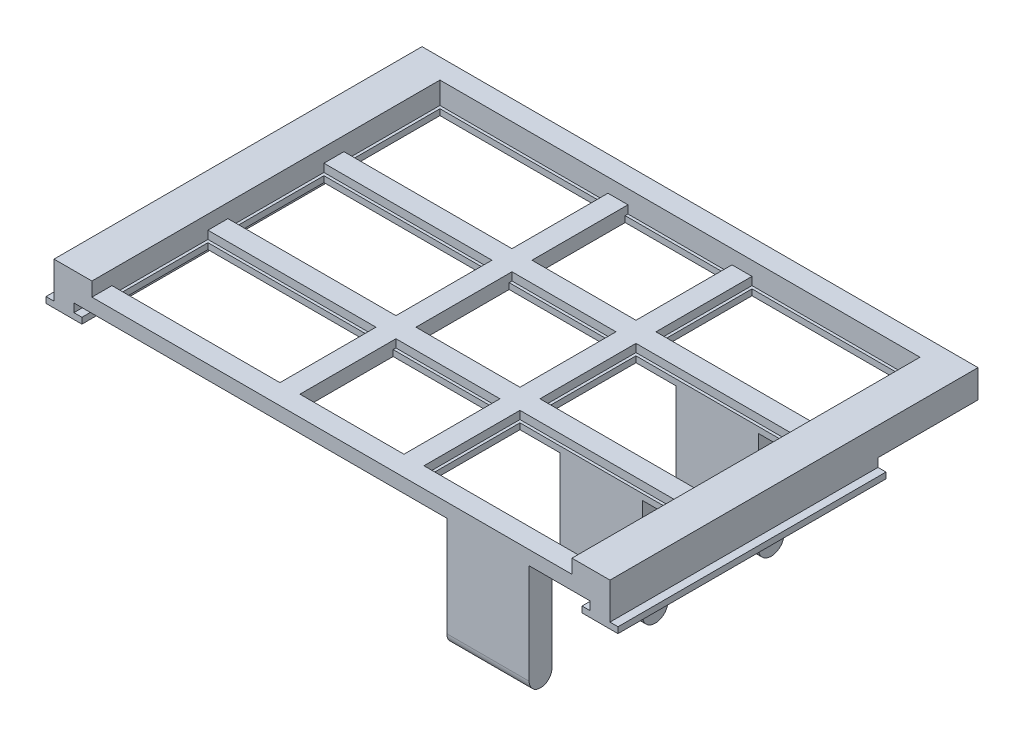
SolidWorks part; units mm, degrees
ref_plane "Front Plane" through (0, 0, 0) normal (0, 0, 1) x (1, 0, 0)
ref_plane "Top Plane" through (0, 0, 0) normal (0, 1, 0) x (1, 0, 0)
ref_plane "Right Plane" through (0, 0, 0) normal (1, 0, 0) x (0, 0, -1)
sketch "Sketch1" plane through (0, 0, 0) normal (0, 1, 0) x (1, 0, 0)
  line L0 (36.2173, -16.1456) -> (36.2173, 113.8544)
  line L1 (50.2173, -6.1456) -> (50.2173, 103.8544)
  line L2 (170.2173, -6.1456) -> (170.2173, 103.8544)
  line L3 (184.2173, -16.1456) -> (184.2173, 113.8544)
  line L4 (36.2173, 113.8544) -> (184.2173, 113.8544)
  line L5 (184.2173, -16.1456) -> (36.2173, -16.1456)
  line L10 (50.2173, 103.8544) -> (170.2173, 103.8544)
  line L12 (170.2173, -6.1456) -> (50.2173, -6.1456)
  line L14 (46.2173, 103.8544) -> (174.2173, 103.8544) construction
  line L15 (174.2173, -6.1456) -> (46.2173, -6.1456) construction
  line L16 (50.2173, -16.1456) -> (50.2173, 113.8544) construction
  line L17 (170.2173, -16.1456) -> (170.2173, 113.8544) construction
  line L18 (46.2173, -6.1456) -> (46.2173, 103.8544) construction
  line L19 (174.2173, -6.1456) -> (174.2173, 103.8544) construction
  line L20 (50.2173, 79.8544) -> (170.2173, 79.8544)
  line L24 (74.2173, 17.8544) -> (74.2173, 79.8544) construction
  line L25 (146.2173, 17.8544) -> (146.2173, 79.8544) construction
  line L26 (146.2173, 17.8544) -> (74.2173, 17.8544) construction
  line L27 (74.2173, 79.8544) -> (146.2173, 79.8544) construction
  line L28 (50.2173, 74.8544) -> (170.2173, 74.8544)
  line L29 (50.2173, 50.8544) -> (170.2173, 50.8544)
  line L30 (50.2173, 45.8544) -> (170.2173, 45.8544)
  line L31 (50.2173, 21.8544) -> (170.2173, 21.8544)
  line L32 (50.2173, 16.8544) -> (170.2173, 16.8544)
  dimension "D1" = 14
  dimension "D2" = 134
  dimension "D3" = 24
  dimension "D4" = 10
  dimension "D5" = 5
  dimension "D6" = 29
  dimension "D7" = 29
extrude "Boss-Extrude2" add sketch "Sketch1" along normal blind 10 contours L5 L3 L4 L0 L2 L12 L1 L10
sketch "Sketch2" plane through (0, 0, 0) normal (0, -1, 0) x (1, 0, 0)
  line L0 (50.2173, -103.8544) -> (170.2173, -103.8544)
  line L1 (50.2173, -103.8544) -> (170.2173, -103.8544) construction
  line L2 (50.2173, 6.1456) -> (170.2173, 6.1456)
  line L3 (170.2173, 6.1456) -> (170.2173, -103.8544) construction
  line L4 (170.2173, 6.1456) -> (50.2173, 6.1456) construction
  line L5 (50.2173, -103.8544) -> (50.2173, 6.1456)
  line L6 (50.2173, 6.1456) -> (50.2173, -103.8544) construction
  line L7 (170.2173, -103.8544) -> (170.2173, 6.1456)
  line L8 (74.2173, -79.8544) -> (146.2173, -79.8544) construction
  line L9 (50.2173, -79.8544) -> (170.2173, -79.8544)
  line L10 (50.2173, -74.8544) -> (170.2173, -74.8544)
  line L11 (74.2173, -79.8544) -> (74.2173, 6.1456) construction
  line L12 (146.2173, -79.8544) -> (146.2173, 6.1456) construction
  line L13 (50.2173, -50.8544) -> (170.2173, -50.8544)
  line L14 (50.2173, -45.8544) -> (170.2173, -45.8544)
  line L15 (50.2173, -21.8544) -> (170.2173, -21.8544)
  line L16 (50.2173, -16.8544) -> (170.2173, -16.8544)
  line L17 (50.9173, -103.1544) -> (169.5173, -103.1544)
  line L18 (169.5173, -103.1544) -> (169.5173, -80.5544)
  line L19 (50.9173, 5.4456) -> (169.5173, 5.4456)
  line L20 (50.9173, -103.1544) -> (50.9173, -80.5544)
  line L21 (50.9173, -74.1544) -> (169.5173, -74.1544)
  line L22 (50.9173, -45.1544) -> (169.5173, -45.1544)
  line L23 (50.9173, -16.1544) -> (169.5173, -16.1544)
  line L24 (50.9173, -80.5544) -> (169.5173, -80.5544)
  line L25 (50.9173, -51.5544) -> (169.5173, -51.5544)
  line L26 (50.9173, -22.5544) -> (169.5173, -22.5544)
  line L27 (50.9173, -74.1544) -> (50.9173, -51.5544)
  line L28 (50.9173, -103.1544) -> (50.9173, 5.4456) construction
  line L29 (50.2173, -74.1544) -> (170.2173, -74.1544) construction
  line L30 (50.2173, -80.5544) -> (170.2173, -80.5544) construction
  line L31 (169.5173, -74.1544) -> (169.5173, -51.5544)
  line L32 (169.5173, -103.1544) -> (169.5173, 5.4456) construction
  line L33 (50.2173, -51.5544) -> (170.2173, -51.5544) construction
  line L34 (169.5173, -45.1544) -> (169.5173, -22.5544)
  line L35 (50.2173, -45.1544) -> (170.2173, -45.1544) construction
  line L36 (50.9173, -45.1544) -> (50.9173, -22.5544)
  line L37 (50.2173, -22.5544) -> (170.2173, -22.5544) construction
  line L38 (169.5173, -16.1544) -> (169.5173, 5.4456)
  line L39 (50.2173, -16.1544) -> (170.2173, -16.1544) construction
  line L40 (50.9173, -16.1544) -> (50.9173, 5.4456)
  line M22 (170.2173, 6.1456) -> (170.2173, -103.8544)
  line M23 (170.2173, -103.8544) -> (50.2173, -103.8544)
  line M24 (50.2173, -103.8544) -> (50.2173, 6.1456)
  line M25 (50.2173, 6.1456) -> (170.2173, 6.1456)
  dimension "D1" = 24
  dimension "D2" = 5
  dimension "D3" = 29
  dimension "D4" = 29
  dimension "D5" = 0.7
  dimension "D6" = 0.7
extrude "Boss-Extrude3" add sketch "Sketch2" against normal blind 1.5 contours L9 L7 L20 L24 L18 L17 M24 M23 | L13 L10 L7 L31 L21 L27 L25 M24 | L15 L14 L7 L22 L36 L26 L34 M24 | L16 L23 L40 L19 L38 M24 M22 M25 | L16 L5 L15 L7 | L14 L5 L13 L7 | L10 L5 L9 L7
sketch "Sketch3" plane through (0, 1.5, 0) normal (0, 1, 0) x (1, 0, 0)
  line L0 (50.2173, 74.8544) -> (170.2173, 74.8544)
  line L3 (50.2173, 79.8544) -> (170.2173, 79.8544)
  line L4 (50.2173, 79.8544) -> (50.2173, 74.8544)
  line L5 (170.2173, 79.8544) -> (170.2173, 74.8544)
  line L6 (50.2173, 45.8544) -> (50.2173, 50.8544)
  line L9 (170.2173, 45.8544) -> (50.2173, 45.8544)
  line L10 (50.2173, 103.8544) -> (50.2173, -6.1456) construction
  line L11 (170.2173, 45.8544) -> (170.2173, 50.8544)
  line L12 (170.2173, -6.1456) -> (170.2173, 103.8544) construction
  line L13 (170.2173, 50.8544) -> (50.2173, 50.8544)
  line L14 (50.2173, 16.8544) -> (50.2173, 21.8544)
  line L16 (170.2173, 16.8544) -> (50.2173, 16.8544)
  line L17 (170.2173, 16.8544) -> (170.2173, 21.8544)
  line L18 (170.2173, -6.1456) -> (170.2173, 103.8544) construction
  line L19 (170.2173, 21.8544) -> (50.2173, 21.8544)
  dimension "D1" = 5
extrude "Boss-Extrude4" add sketch "Sketch3" along normal blind 2 contours L19 L14 L16 L17 | L13 L6 L9 L11 | L5 L0 L4 L3
sketch "Sketch4" plane through (0, 0, 0) normal (0, -1, 0) x (-1, 0, 0)
  line L0 (-50.2173, 103.8544) -> (-50.2173, -6.1456)
  line L1 (-170.2173, -6.1456) -> (-50.2173, -6.1456) construction
  line L2 (-50.2173, -6.1456) -> (-50.2173, 103.8544) construction
  line L3 (-92.2173, 103.8544) -> (-92.2173, -6.1456)
  line L4 (-87.2173, 103.8544) -> (-87.2173, -6.1456)
  line L5 (-87.2173, 103.8544) -> (-92.2173, 103.8544)
  line L6 (-92.2173, -6.1456) -> (-87.2173, -6.1456)
  line L7 (-170.2173, -6.1456) -> (-170.2173, 103.8544)
  line L8 (-128.2173, -6.1456) -> (-128.2173, 103.8544)
  line L9 (-123.2173, -6.1456) -> (-123.2173, 103.8544)
  line L10 (-123.2173, 103.8544) -> (-128.2173, 103.8544)
  line L11 (-128.2173, -6.1456) -> (-123.2173, -6.1456)
  dimension "D1" = 42
  dimension "D2" = 5
  dimension "D3" = 42
  dimension "D4" = 5
extrude "Boss-Extrude5" add sketch "Sketch4" against normal blind 3.5 contours L4 L6 L3 L5 | L9 L10 L8 L11
sketch "Sketch5" plane through (0, 0, 0) normal (0, -1, 0) x (-1, 0, 0)
  line L1 (-92.2173, 80.5544) -> (-92.2173, 103.1544)
  line L2 (-92.2173, 103.1544) -> (-87.2173, 103.1544)
  line L14 (-87.2173, 16.1544) -> (-92.2173, 16.1544)
  line L15 (-92.2173, 16.8544) -> (-92.2173, -6.1456) construction
  line L16 (-92.2173, 16.1544) -> (-92.2173, -5.4456)
  line L17 (-92.2173, -5.4456) -> (-87.2173, -5.4456)
  line L18 (-87.2173, 16.8544) -> (-87.2173, -6.1456) construction
  line L19 (-87.2173, -5.4456) -> (-87.2173, 16.1544)
  line L21 (-87.2173, 22.5544) -> (-92.2173, 22.5544)
  line L22 (-92.2173, 22.5544) -> (-92.2173, 45.1544)
  line L23 (-92.2173, 45.1544) -> (-87.2173, 45.1544)
  line L24 (-87.2173, 103.1544) -> (-87.2173, 80.5544)
  line L25 (-87.2173, 22.5544) -> (-87.2173, 45.1544)
  line L26 (-87.2173, 51.5544) -> (-92.2173, 51.5544)
  line L27 (-92.2173, 51.5544) -> (-92.2173, 74.1544)
  line L28 (-92.2173, 74.1544) -> (-87.2173, 74.1544)
  line L29 (-87.2173, 74.1544) -> (-87.2173, 51.5544)
  line L30 (-87.2173, 80.5544) -> (-92.2173, 80.5544)
extrude "Cut-Extrude1" cut sketch "Sketch5" against normal blind 10
sketch "Sketch6" plane through (0, 1.5, 0) normal (0, 1, 0) x (1, 0, 0)
  line L0 (87.2173, 103.8544) -> (92.2173, 103.8544)
  line L1 (92.2173, 103.8544) -> (92.2173, 103.1544)
  line L2 (92.2173, 103.8544) -> (92.2173, 103.1544) construction
  line L3 (92.2173, 103.1544) -> (87.2173, 103.1544) construction
  line L4 (92.2173, 103.1544) -> (87.2173, 103.1544)
  line L5 (87.2173, 103.1544) -> (87.2173, 103.8544)
  line L6 (92.2173, 80.5544) -> (87.2173, 80.5544)
  line L7 (87.2173, 80.5544) -> (87.2173, 79.8544)
  line L8 (87.2173, 79.8544) -> (92.2173, 79.8544)
  line L9 (92.2173, 79.8544) -> (92.2173, 80.5544)
  line L10 (87.2173, 74.8544) -> (92.2173, 74.8544)
  line L11 (92.2173, 74.8544) -> (92.2173, 74.1544)
  line L12 (92.2173, 74.1544) -> (87.2173, 74.1544) construction
  line L13 (92.2173, 74.1544) -> (123.2173, 74.1544) construction
  line L14 (92.2173, 74.1544) -> (87.2173, 74.1544)
  line L15 (87.2173, 74.8544) -> (87.2173, 74.1544) construction
  line L16 (87.2173, 74.1544) -> (87.2173, 74.8544)
  line L17 (87.2173, 51.5544) -> (92.2173, 51.5544)
  line L18 (92.2173, 51.5544) -> (92.2173, 50.8544)
  line L19 (92.2173, 50.8544) -> (87.2173, 50.8544)
  line L20 (87.2173, 50.8544) -> (87.2173, 51.5544)
  line L21 (92.2173, 45.8544) -> (87.2173, 45.8544)
  line L22 (87.2173, 45.8544) -> (87.2173, 45.1544)
  line L23 (92.2173, 45.1544) -> (87.2173, 45.1544) construction
  line L24 (87.2173, 45.1544) -> (92.2173, 45.1544)
  line L25 (92.2173, 45.1544) -> (92.2173, 45.8544)
  line L26 (87.2173, 22.5544) -> (92.2173, 22.5544)
  line L27 (92.2173, 22.5544) -> (92.2173, 21.8544)
  line L28 (92.2173, 21.8544) -> (87.2173, 21.8544)
  line L29 (87.2173, 21.8544) -> (87.2173, 22.5544)
  line L30 (87.2173, 16.8544) -> (92.2173, 16.8544)
  line L31 (92.2173, 16.8544) -> (92.2173, 16.1544)
  line L32 (92.2173, 16.1544) -> (87.2173, 16.1544) construction
  line L33 (92.2173, 16.1544) -> (87.2173, 16.1544)
  line L34 (87.2173, 16.8544) -> (87.2173, 16.1544) construction
  line L35 (87.2173, 16.1544) -> (87.2173, 16.8544)
  line L36 (87.2173, -5.4456) -> (92.2173, -5.4456)
  line L37 (92.2173, -5.4456) -> (92.2173, -6.1456)
  line L38 (92.2173, -6.1456) -> (87.2173, -6.1456)
  line L39 (87.2173, -6.1456) -> (87.2173, -5.4456)
extrude "Cut-Extrude2" cut sketch "Sketch6" along normal blind 2
sketch "Sketch7" plane through (0, 0, 0) normal (0, -1, 0) x (-1, 0, 0)
  line L0 (-92.2173, 79.8544) -> (-97.2173, 79.8544)
  line L3 (-92.2173, 103.8544) -> (-92.2173, 79.8544)
  line L4 (-97.2173, 103.8544) -> (-97.2173, 79.8544)
  line L5 (-97.2173, 103.8544) -> (-92.2173, 103.8544)
  line L6 (-92.2173, 74.8544) -> (-92.2173, 50.8544)
  line L7 (-97.2173, 74.8544) -> (-97.2173, 50.8544)
  line L8 (-92.2173, 50.8544) -> (-97.2173, 50.8544)
  line L9 (-97.2173, 74.8544) -> (-92.2173, 74.8544)
  line L10 (-97.2173, 16.8544) -> (-97.2173, -6.1456)
  line L11 (-97.2173, 16.8544) -> (-92.2173, 16.8544)
  line L12 (-92.2173, 21.8544) -> (-97.2173, 21.8544)
  line L13 (-97.2173, 45.8544) -> (-92.2173, 45.8544)
  line L15 (-97.2173, 45.8544) -> (-97.2173, 21.8544)
  line L16 (-92.2173, 16.8544) -> (-92.2173, -6.1706)
  line L17 (-92.2173, 45.8544) -> (-92.2173, 21.8544)
  line L18 (-92.2173, -6.1706) -> (-97.2173, -6.1456)
  line L19 (-50.2173, -6.1456) -> (-123.2173, -6.1456) construction
  dimension "D2" = 5
extrude "Boss-Extrude7" add sketch "Sketch7" against normal blind 3.5
sketch "Sketch8" plane through (0, 0, 0) normal (0, -1, 0) x (-1, 0, 0)
  line L0 (-92.2173, 103.1544) -> (-92.2173, 80.5544)
  line L1 (-92.2173, 103.1544) -> (-91.5173, 103.1544)
  line L2 (-50.9173, 103.1544) -> (-92.2173, 103.1544) construction
  line L3 (-91.5173, 103.1544) -> (-91.5173, 80.5544)
  line L4 (-50.9173, 80.5544) -> (-92.2173, 80.5544) construction
  line L5 (-91.5173, 80.5544) -> (-92.2173, 80.5544)
  line L6 (-91.5173, 74.1544) -> (-91.5173, 51.5544)
  line L7 (-92.2173, 74.1544) -> (-91.5173, 74.1544)
  line L8 (-91.5173, 51.5544) -> (-92.2173, 51.5544)
  line L9 (-92.2173, 74.1544) -> (-92.2173, 51.5544)
  line L10 (-91.5173, 22.5544) -> (-92.2173, 22.5544)
  line L11 (-92.2173, 45.1544) -> (-92.2173, 22.5544)
  line L12 (-92.2173, 45.1544) -> (-91.5173, 45.1544)
  line L13 (-91.5173, 45.1544) -> (-91.5173, 22.5544)
extrude "Boss-Extrude8" add sketch "Sketch8" against normal blind 1.5
sketch "Sketch9" plane through (0, 0, 0) normal (0, -1, 0) x (-1, 0, 0)
  line L14 (-50.2173, 16.8544) -> (-92.2173, 16.8544)
  line L15 (-170.2173, -6.1456) -> (-170.2173, 103.8544) construction
  line L16 (-170.2173, 16.8544) -> (-128.2173, 16.8544) construction
  line L36 (-170.2173, -6.1456) -> (-128.2173, -6.1456)
  line L37 (-50.2173, -6.1456) -> (-92.2173, -6.1456) construction
  line L40 (-170.2173, -6.1456) -> (-50.2173, -6.1456) construction
  line L41 (-170.2173, -6.1456) -> (-170.2173, 16.8544)
  line L42 (-50.2173, 16.8544) -> (-50.2173, -6.1456)
  line L43 (-50.9173, 16.1544) -> (-92.2173, 16.1544)
  line L44 (-92.2173, 16.1544) -> (-92.2173, 16.8544)
  line L45 (-92.2173, -6.1456) -> (-92.2173, -5.4456)
  line L46 (-92.2173, -5.4456) -> (-50.9173, -5.4456)
  line L47 (-50.9173, -5.4456) -> (-50.9173, 16.1544)
  line L48 (-97.2173, 16.8544) -> (-97.2173, 16.1544)
  line L49 (-97.2173, 16.1544) -> (-123.2173, 16.1544)
  line L50 (-123.2173, 16.1544) -> (-123.2173, 16.8544)
  line L51 (-123.2173, -5.4456) -> (-97.2173, -5.4456)
  line L52 (-97.2173, -5.4456) -> (-97.2173, -6.1456)
  line L53 (-97.2173, 16.8544) -> (-97.2173, -6.1456) construction
  line L54 (-97.2173, -6.1456) -> (-123.2173, -6.1456)
  line L55 (-123.2173, -6.1456) -> (-123.2173, 16.8544) construction
  line L56 (-123.2173, -6.1456) -> (-123.2173, -5.4456)
  line L57 (-128.2173, 16.8544) -> (-128.2173, 16.1544)
  line L58 (-128.2173, 16.1544) -> (-169.5173, 16.1544)
  line L59 (-169.5173, 16.1544) -> (-169.5173, -5.4456)
  line L60 (-169.5173, -5.4456) -> (-128.2173, -5.4456)
  line L61 (-128.2173, -5.4456) -> (-128.2173, -6.1456)
  line L62 (-97.2173, 16.8544) -> (-123.2173, 16.8544)
  line L63 (-92.2173, -6.1456) -> (-50.2173, -6.1456)
  line L65 (-128.2173, 16.8544) -> (-170.2173, 16.8544)
extrude "Cut-Extrude3" cut sketch "Sketch9" against normal blind 1.5
sketch "Sketch10" plane through (0, 0, 0) normal (0, -1, 0) x (-1, 0, 0)
  line L0 (-128.2173, 103.1544) -> (-128.2173, 80.5544)
  line L1 (-128.2173, 103.1544) -> (-128.9173, 103.1544)
  line L2 (-128.2173, 103.1544) -> (-169.5173, 103.1544) construction
  line L3 (-128.2173, 80.5544) -> (-128.9173, 80.5544)
  line L4 (-128.2173, 80.5544) -> (-169.5173, 80.5544) construction
  line L5 (-128.9173, 80.5544) -> (-128.9173, 103.1544)
  line L6 (-128.9173, 51.5544) -> (-128.9173, 74.1544)
  line L7 (-128.2173, 74.1544) -> (-128.2173, 51.5544)
  line L8 (-128.2173, 51.5544) -> (-128.9173, 51.5544)
  line L9 (-128.2173, 74.1544) -> (-128.9173, 74.1544)
  line L10 (-128.2173, 22.5544) -> (-128.9173, 22.5544)
  line L11 (-128.9173, 22.5544) -> (-128.9173, 45.1544)
  line L12 (-128.2173, 45.1544) -> (-128.2173, 22.5544)
  line L13 (-128.2173, 45.1544) -> (-128.9173, 45.1544)
extrude "Boss-Extrude9" add sketch "Sketch10" against normal blind 1.5
sketch "Sketch11" plane through (0, 0, 0) normal (0, -1, 0) x (-1, 0, 0)
  line L0 (-45.7173, 13.8544) -> (-45.7173, 83.8544)
  line L1 (-40.7173, 13.8544) -> (-40.7173, 83.8544)
  line L2 (-179.7173, 13.8544) -> (-179.7173, 83.8544)
  line L8 (-40.7173, 13.8544) -> (-45.7173, 13.8544)
  line L9 (-40.7173, 83.8544) -> (-45.7173, 83.8544)
  line L10 (-40.7173, -16.1456) -> (-40.7173, 113.8544) construction
  line L11 (-45.7173, -16.1456) -> (-45.7173, 113.8544) construction
  line L12 (-174.7173, 13.8544) -> (-174.7173, 83.8544)
  line L13 (-174.7173, 13.8544) -> (-179.7173, 13.8544)
  line L14 (-174.7173, 83.8544) -> (-179.7173, 83.8544)
extrude "Boss-Extrude10" add sketch "Sketch11" along normal blind 3
sketch "Sketch12" plane through (0, 10, 0) normal (0, 1, 0) x (1, 0, 0)
  line L4 (36.2173, -16.1456) -> (40.7367, -16.1456)
  line L12 (184.2173, -16.1456) -> (36.2173, -16.1456) construction
  line L13 (40.7367, -16.1456) -> (40.7367, 113.8544)
  line L14 (36.2173, 113.8544) -> (184.2173, 113.8544) construction
  line L15 (40.7367, 113.8544) -> (36.2173, 113.8544)
  line L16 (36.2173, 113.8544) -> (36.2173, -16.1456)
  line L17 (184.2173, -16.1456) -> (179.7173, -16.1456)
  line L18 (179.7173, -16.1456) -> (179.7173, 113.8544)
  line L19 (179.7173, 113.8544) -> (184.2173, 113.8544)
  line L20 (184.2173, 113.8544) -> (184.2173, -16.1456)
extrude "Cut-Extrude4" cut sketch "Sketch12" against normal blind 20
sketch "Sketch13" plane through (0, 0, 0) normal (0, -1, 0) x (-1, 0, 0)
  line L0 (-40.7367, 13.8544) -> (-179.7173, 13.8544)
  line L1 (-179.7173, 13.8544) -> (-179.7173, -16.1456)
  line L2 (-179.7173, -16.1456) -> (-40.7367, -16.1456)
  line L3 (-40.7367, -16.1456) -> (-40.7367, 13.8544)
  line L4 (-40.7367, 113.8544) -> (-40.7367, 108.8544)
  line L5 (-40.7367, 83.8544) -> (-40.7367, 113.8544) construction
  line L6 (-40.7367, 108.8544) -> (-179.7173, 108.8544)
  line L7 (-179.7173, 113.8544) -> (-179.7173, 83.8544) construction
  line L8 (-179.7173, 108.8544) -> (-179.7173, 113.8544)
  line L9 (-179.7173, 113.8544) -> (-40.7367, 113.8544)
extrude "Cut-Extrude5" cut sketch "Sketch13" against normal blind 20
sketch "Sketch14" plane through (0, 0, 0) normal (0, -1, 0) x (-1, 0, 0)
  line L0 (-179.7173, 16.8544) -> (-40.7367, 16.8544)
  line L1 (-179.7173, 83.8544) -> (-179.7173, 13.8544) construction
  line L2 (-40.7367, 13.8544) -> (-40.7367, 83.8544) construction
  line L3 (-40.7367, 16.8544) -> (-40.7367, 13.8544)
  line L4 (-40.7367, 13.8544) -> (-179.7173, 13.8544)
  line L5 (-179.7173, 13.8544) -> (-179.7173, 16.8544)
extrude "Cut-Extrude6" cut sketch "Sketch14" against normal blind 20
sketch "Sketch15" plane through (0, -3, 0) normal (0, -1, 0) x (-1, 0, 0)
  line L0 (-45.7173, 16.8544) -> (-40.7367, 16.8544)
  line L1 (-40.7367, 16.8544) -> (-40.7367, 13.8544)
  line L2 (-40.7367, 13.8544) -> (-45.7173, 13.8544)
  line L3 (-45.7173, 13.8544) -> (-40.7367, 13.8544) construction
  line L4 (-45.7173, 83.8544) -> (-45.7173, 13.8544) construction
  line L5 (-45.7173, 13.8544) -> (-45.7173, 16.8544)
  line L6 (-174.7173, 16.8544) -> (-179.7173, 16.8544)
  line L7 (-179.7173, 83.8544) -> (-179.7173, 13.8544) construction
  line L8 (-179.7173, 16.8544) -> (-179.7173, 13.8544)
  line L9 (-179.7173, 13.8544) -> (-174.7173, 13.8544)
  line L10 (-179.7173, 13.8544) -> (-174.7173, 13.8544) construction
  line L11 (-174.7173, 13.8544) -> (-174.7173, 83.8544) construction
  line L12 (-174.7173, 13.8544) -> (-174.7173, 16.8544)
extrude "Cut-Extrude7" cut sketch "Sketch15" against normal blind 20
sketch "Sketch16" plane through (0, 0, -16.8544) normal (0, 0, 1) x (1, 0, 0)
  line L0 (40.7367, 10) -> (40.7367, 7)
  line L2 (40.7367, -3) -> (40.7367, 10) construction
  line L3 (40.7367, 7) -> (179.7173, 7)
  line L4 (179.7173, 10) -> (179.7173, -3) construction
  line L5 (179.7173, 7) -> (179.7173, 10)
  line L6 (179.7173, 10) -> (40.7367, 10)
extrude "Cut-Extrude8" cut sketch "Sketch16" against normal blind 200
sketch "Sketch17" plane through (0, 0, 0) normal (0, -1, 0) x (-1, 0, 0)
  line L0 (-138.9173, 74.1544) -> (-159.5173, 74.1544)
  line L1 (-138.9173, 74.1544) -> (-138.9173, 80.5544)
  line L2 (-159.5173, 80.5544) -> (-138.9173, 80.5544)
  line L4 (-159.5173, 74.1544) -> (-159.5173, 80.5544)
  line L5 (-159.5173, 45.1544) -> (-159.5173, 51.5544)
  line L6 (-138.9173, 45.1544) -> (-138.9173, 51.5544)
  line L7 (-159.5173, 51.5544) -> (-138.9173, 51.5544)
  line L8 (-138.9173, 45.1544) -> (-159.5173, 45.1544)
  line L9 (-159.5173, 16.8544) -> (-159.5173, 22.5544)
  line L11 (-138.9173, 16.8544) -> (-138.9173, 22.5544)
  line L12 (-138.9173, 16.8544) -> (-159.5173, 16.8544)
  line L13 (-138.9173, 22.5544) -> (-159.5173, 22.5544)
  line L14 (-128.9173, 22.5544) -> (-169.5173, 22.5544) construction
extrude "Boss-Extrude11" add sketch "Sketch17" along normal blind 10
sketch "Sketch18" plane through (138.9173, 0, 0) normal (-1, 0, 0) x (0, 0, 1)
  line L0 (-16.8544, -10) -> (-22.5544, -10) construction
  line L1 (-45.1544, -10) -> (-51.5544, -10) construction
  line L2 (-74.1544, -10) -> (-80.5544, -10) construction
  line L3 (-22.5544, -10) -> (-16.8544, -10)
  line L4 (-45.1544, -10) -> (-51.5544, -10)
  line L5 (-74.1544, -10) -> (-80.5544, -10)
  arc A0 (-22.5544, -10) -> (-16.8544, -10) centre (-19.7044, -10) ccw
  arc A1 (-51.5544, -10) -> (-45.1544, -10) centre (-48.3544, -10) ccw
  arc A2 (-80.5544, -10) -> (-74.1544, -10) centre (-77.3544, -10) ccw
extrude "Boss-Extrude12" add sketch "Sketch18" against normal blind 20.6
sketch "Sketch19" plane through (138.9173, 0, 0) normal (-1, 0, 0) x (0, 0, 1)
  line L0 (-16.8544, -10) -> (-16.8544, -25)
  line L1 (-22.5544, -10) -> (-22.5544, -25)
  line L2 (-45.1544, -10) -> (-45.1544, -25)
  line L3 (-51.5544, -10) -> (-51.5544, -25)
  line L4 (-74.1544, -10) -> (-74.1544, -25)
  line L5 (-80.5544, -10) -> (-80.5544, -25)
  line L6 (-45.1544, -10) -> (-51.5544, -10)
  line L7 (-74.1544, -10) -> (-80.5544, -10)
  arc A0 (-22.5544, -25) -> (-16.8544, -25) centre (-19.7044, -25) ccw
  arc A1 (-16.8544, -10) -> (-22.5544, -10) centre (-19.7044, -10) cw
  arc A2 (-51.5544, -10) -> (-45.1544, -10) centre (-48.3544, -10) ccw construction
  arc A3 (-51.5544, -25) -> (-45.1544, -25) centre (-48.3544, -25) ccw
  arc A4 (-74.1544, -25) -> (-80.5544, -25) centre (-77.3544, -25) cw
extrude "Boss-Extrude13" add sketch "Sketch19" against normal blind 20.6
sketch "Sketch20" plane through (0, -3, 0) normal (0, -1, 0) x (-1, 0, 0)
  line L0 (-179.7173, 83.8544) -> (-174.7173, 83.8544)
  line L1 (-174.7173, 83.8544) -> (-174.7173, 16.8544)
  line L2 (-174.7173, 16.8544) -> (-179.7173, 16.8544)
  line L3 (-179.7173, 16.8544) -> (-179.7173, 83.8544)
  line L4 (-45.7173, 83.8544) -> (-40.7367, 83.8544)
  line L5 (-40.7367, 83.8544) -> (-40.7367, 16.8544)
  line L6 (-40.7367, 16.8544) -> (-45.7173, 16.8544)
  line L7 (-45.7173, 16.8544) -> (-45.7173, 83.8544)
extrude "Cut-Extrude9" cut sketch "Sketch20" against normal blind 0.9
sketch "Sketch21" plane through (0, -2.1, 0) normal (0, -1, 0) x (-1, 0, 0)
  line L2 (-47.7173, 83.8544) -> (-38.7367, 83.8544)
  line L3 (-47.7173, 83.8544) -> (-47.7173, 16.8544)
  line L4 (-38.7367, 83.8544) -> (-38.7367, 16.8544)
  line L5 (-38.7367, 16.8544) -> (-47.7173, 16.8544)
  line L6 (-172.7367, 83.8544) -> (-172.7367, 16.8544)
  line L7 (-172.7367, 16.8544) -> (-181.7173, 16.8544)
  line L9 (-181.7173, 83.8544) -> (-172.7367, 83.8544)
  line L11 (-181.7173, 83.8544) -> (-181.7173, 16.8544)
extrude "Boss-Extrude14" add sketch "Sketch21" along normal blind 1.5
